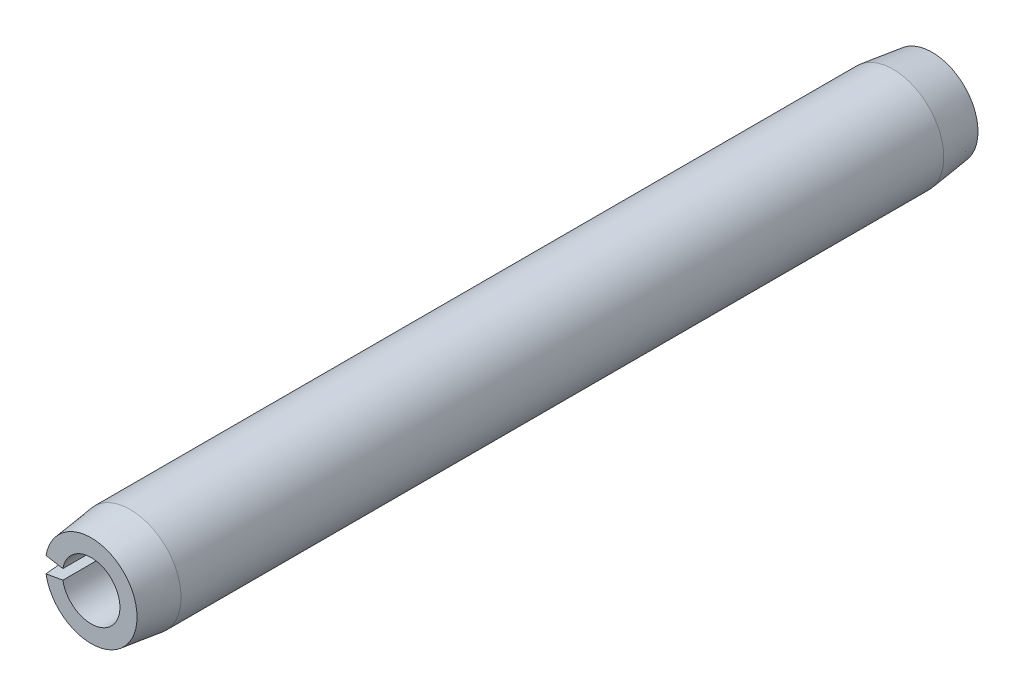
SolidWorks part; units mm, degrees
material "AISI 316 Annealed Stainless Steel Bar (SS)"
ref_plane "Front Plane" through (0, 0, 0) normal (0, 0, 1) x (1, 0, 0)
ref_plane "Top Plane" through (0, 0, 0) normal (0, 1, 0) x (1, 0, 0)
ref_plane "Right Plane" through (0, 0, 0) normal (1, 0, 0) x (0, 0, -1)
sketch "Sketch1" plane through (0, 0, 0) normal (0, 0, 1) x (1, 0, 0)
  line L0 (0.5969, 0) -> (1.0541, 0) construction
  line L1 (-1.0381, 0.183) -> (-0.5878, 0.1037)
  line L2 (-0.5878, -0.1037) -> (-1.0381, -0.183)
  arc A0 (-1.0381, -0.183) -> (-1.0381, 0.183) centre (0, 0) ccw
  arc A1 (-0.5878, -0.1037) -> (-0.5878, 0.1037) centre (0, 0) ccw
  dimension "OD" = 2.1082
  dimension "Wall thickness" = 0.4572
  dimension "D3" = 20
extrude "Extrude1" add sketch "Sketch1" along normal mid plane 17.4625
sketch "Sketch2" plane through (0, 0, 0) normal (1, 0, 0) x (0, 0, -1)
  line L0 (0, -1.0541) -> (0, 1.0541) construction
  line L1 (8.7312, 0) -> (-8.7312, 0) construction
  line L2 (8.7312, -0.5969) -> (8.7312, 0.5969) construction
  line L3 (8.7312, 1.0541) -> (-8.7312, 1.0541) construction
  line L4 (8.7312, 1.0541) -> (8.7312, 0.9525)
  line L5 (8.7312, 0.9525) -> (7.9184, 1.0541)
  line L6 (7.9184, 1.0541) -> (8.7312, 1.0541)
  line L7 (8.7312, -1.0541) -> (8.7312, 1.0541) construction
  line L8 (-7.9184, 1.0541) -> (-8.7312, 1.0541)
  line L9 (-8.7312, 0.9525) -> (-7.9184, 1.0541)
  line L10 (-8.7312, 1.0541) -> (-8.7312, 0.9525)
  line L11 (7.9184, -1.0541) -> (8.7312, -1.0541) construction
  line L12 (8.7312, -0.9525) -> (7.9184, -1.0541) construction
  line L13 (8.7312, -1.0541) -> (8.7312, -0.9525) construction
  dimension "B" = 1.905
  dimension "Chamfer max" = 0.8128
revolve "Cut-Revolve1" cut sketch "Sketch2" angle 360 about L1
sketch "Sketch3" plane through (0, 0, 0) normal (0, 0, 1) x (1, 0, 0)
  line L0 (0.5969, 0) -> (1.0541, 0) construction
  line L1 (0.5969, 0) -> (1.0541, 0)
  circle A0 centre (0, 0) radius 1.0541
  circle A1 centre (0, 0) radius 0.5969
  arc A2 (-1.0381, -0.183) -> (-1.0381, 0.183) centre (0, 0) ccw construction
  arc A3 (-0.5878, -0.1037) -> (-0.5878, 0.1037) centre (0, 0) ccw construction
